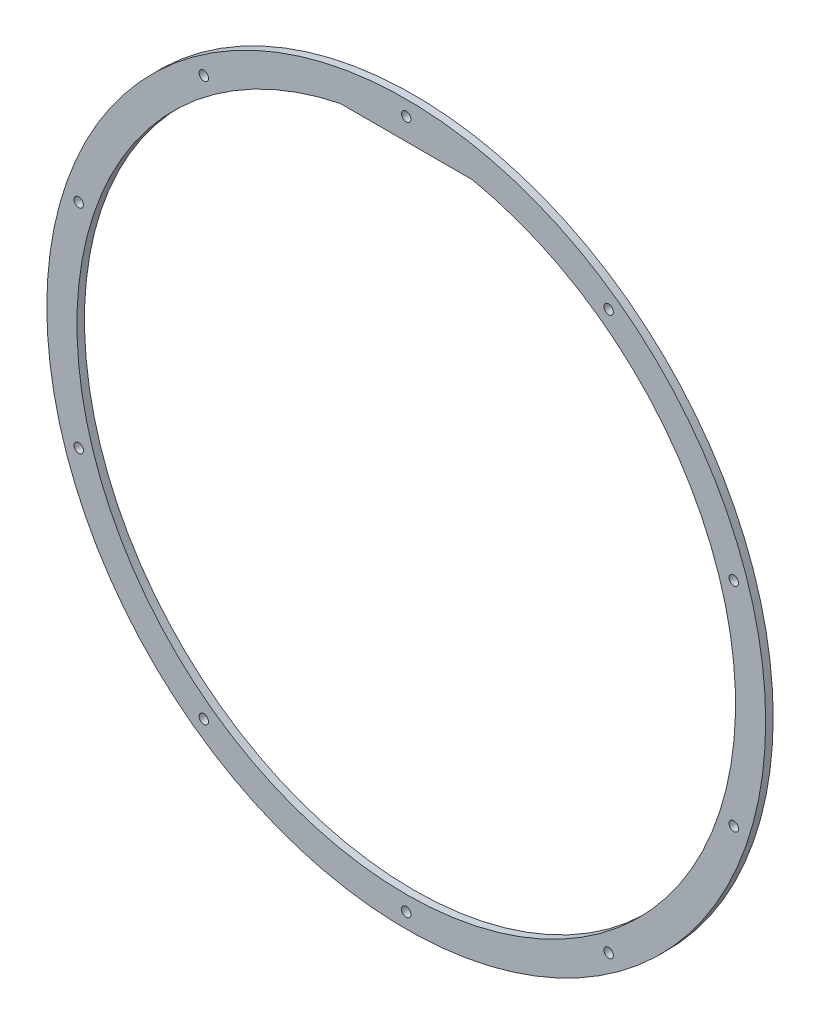
SolidWorks part; units mm, degrees
material "AISI 316 Stainless Steel Sheet (SS)"
ref_plane "Front Plane" through (0, 0, 0) normal (0, 0, 1) x (1, 0, 0)
ref_plane "Top Plane" through (0, 0, 0) normal (0, 1, 0) x (1, 0, 0)
ref_plane "Right Plane" through (0, 0, 0) normal (1, 0, 0) x (0, 0, -1)
sketch "Sketch1" plane through (0, 0, 0) normal (0, 0, 1) x (1, 0, 0)
  line L1 (-35, 171.4643) -> (35, 171.4643)
  arc A1 (-35, 171.4643) -> (35, 171.4643) centre (0, 0) ccw
  circle A2 centre (0, 0) radius 191
  dimension "D1" = 175
  dimension "D3" = 16
  dimension "D2" = 70
extrude "Boss-Extrude1" add sketch "Sketch1" along normal blind 4
hole_wizard "M6 Tapped Hole1" positions "Sketch2" profile "Sketch3" tap size "M6" standard "ISO" end condition through all
sketch "Sketch2" plane through (0, 0, 4) normal (0, 0, 1) x (1, 0, 0)
  circle A3 centre (0, 0) radius 183
  circle A4 centre (0, 0) radius 183
  point P10 (0, 183)
  dimension "D1" = 8
sketch "Sketch3" plane through (0, 183, 4) normal (1, 0, 0) x (0, -1, 0)
  line L0 (0, 0) -> (0, 4)
  line L1 (0, 4) -> (2.5, 4)
  line L2 (2.5, 4) -> (2.5, 0)
  line L5 (2.5, 0) -> (0, 0)
  line L11 (0, -6.35) -> (0, 107.95) construction
  dimension "Thru Tap Drill Dia." = 5
  dimension "Thru Tap Drill Depth" = 4
pattern_circular "CirPattern1" count 10 over 360 about axis through (0, 0, 0) along (0, 0, 1) of "M6 Tapped Hole1"
